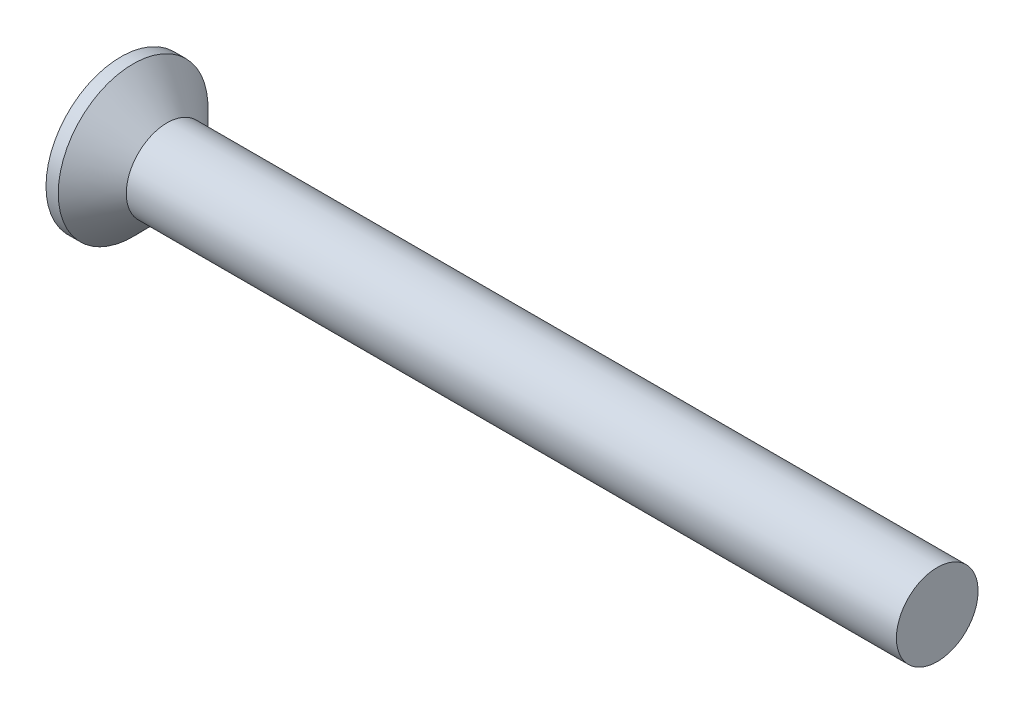
SolidWorks part; units mm, degrees
revolve "Base-Revolve" add sketch "BodySke" angle 360 about L5
sketch "BodySke" plane through (0, 0, 0) normal (0, 0, 1) x (1, 0, 0)
  line L0 (0, 0) -> (0, 2.75)
  line L1 (0, 2.75) -> (0.45, 2.75)
  line L2 (1.7, 1.5) -> (30, 1.5)
  line L3 (30, 1.5) -> (30, 0)
  line L4 (30, 0) -> (0, 0)
  line L5 (-6.35, 0) -> (82.55, 0) construction
  line L6 (1.7, -1.5) -> (30, -1.5) construction
  line L7 (0.45, -2.75) -> (1.7, -1.5) construction
  line L8 (0.45, 2.75) -> (1.7, 1.5)
  line L9 (0, -2.75) -> (0.45, -2.75) construction
  line L10 (2.2, 3.0875) -> (2.2, -6.4375) construction
  line L11 (0, 6.35) -> (0, -3.175) construction
  dimension "Diameter" = 3
  dimension "Length" = 30
  dimension "Head_ht" = 1.7
  dimension "Head_dia" = 5.5
  dimension "Head_ang" = 90
  dimension "D6" = 0.45
  dimension "Advance" = 0.5
  dimension "Thread_nom" = 30
cosmetic thread "ThreadCosmetic" parameters "Thread_length"=27.8, "Thread_minor"=2.439
extrude "Slot" [suppressed] cut sketch "Sketch2" against normal blind 0.9
sketch "Sketch2" plane through (0, 0, 0) normal (-1, 0, 0) x (0, 0, 1)
  line L0 (-2.75, -0.5) -> (2.75, -0.5)
  line L1 (-2.75, -0.5) -> (-2.75, 0.5)
  line L2 (2.75, 0.5) -> (-2.75, 0.5)
  line L3 (2.75, 0.5) -> (2.75, -0.5)
  dimension "Slot_width" = 1
  dimension "D1" = 0.5
  dimension "D2" = 5.5
  dimension "D3" = 2.75
ref_plane "Plane1" through (0, 0, 0) normal (0, 0, 1) x (1, 0, 0)
ref_plane "Plane2" through (0, 0, 0) normal (0, 1, 0) x (1, 0, 0)
ref_plane "Plane3" through (0, 0, 0) normal (1, 0, 0) x (0, 0, -1)
sketch "Sketch3" plane through (0, 0, 0) normal (-1, 0, 0) x (0, 0, 1)
  line L0 (-0.395, 1.55) -> (0.395, 1.55)
  line L1 (0.395, 1.55) -> (0.395, -1.55)
  line L2 (0.395, -1.55) -> (-0.395, -1.55)
  line L3 (-0.395, -1.55) -> (-0.395, 1.55)
  dimension "Cross_dia" = 3.1
  dimension "Cross_width" = 0.79
  dimension "D1" = 1.55
  dimension "D2" = 0.395
ref_plane "Plane4" through (2.08, 0, 0) normal (-1, 0, 0) x (0, 0, 1)
sketch "Sketch4" plane through (2.08, 0, 0) normal (-1, 0, 0) x (0, 0, 1)
  line L0 (-0.1975, 0.1975) -> (0.1975, 0.1975)
  line L3 (0.1975, 0.1975) -> (0.1975, -0.1975)
  line L4 (0.1975, -0.1975) -> (-0.1975, -0.1975)
  line L5 (-0.1975, -0.1975) -> (-0.1975, 0.1975)
  dimension "D2" = 0.395
  dimension "D1" = 0.395
  dimension "D3" = 0.1975
  dimension "D4" = 0.1975
loft "Cross" cut profiles "Sketch3", "Sketch4"
pattern_circular "CirPattern1" count 2 every 90 about axis through (0, 0, 0) along (1, 0, 0) of "Cross"
sketch "ThdSchSke" plane through (0, 0, 0) normal (0, 0, 1) x (1, 0, 0)
  line L0 (2.2, -1.2195) -> (2.0036, -1.5)
  line L1 (2.2, -1.2195) -> (2.3964, -1.5)
  line L2 (2.3964, -1.5) -> (2.3964, -1.875)
  line L3 (-3.175, 0) -> (5.1513, 0) construction
  line L5 (2.3964, -1.875) -> (2.0036, -1.875)
  line L6 (2.0036, -1.875) -> (2.0036, -1.5)
  line L7 (0, 2.75) -> (0, -2.75) construction
  dimension "Diameter" = 3
  dimension "Thread_minor" = 2.439
  dimension "Start" = 2.2
revolve "ThreadSchematic" [suppressed] cut sketch "ThdSchSke" angle 360 about L3
pattern_linear "ThdSchPat" [suppressed]
equation "\"D1@Sketch3\" = \"Cross_dia@Sketch3\" / 2"
equation "\"D2@Sketch3\" = \"Cross_width@Sketch3\" / 2"
equation "\"D1@Sketch4\" = \"Cross_width@Sketch3\" *.5"
equation "\"D2@Sketch4\" = \"D1@Sketch4\""
equation "\"D4@Sketch4\" = \"D2@Sketch4\" / 2"
equation "\"D3@Sketch4\" = \"D1@Sketch4\" / 2"
equation "\"D1@Sketch2\" = \"Slot_width@Sketch2\" / 2"
equation "\"D2@Sketch2\" = \"Head_dia@BodySke\""
equation "\"D3@Sketch2\" = \"D2@Sketch2\" / 2"
equation "\"Thread_length@ThreadCosmetic\" = ((sgn( (\"Length@BodySke\" - \"Advance@BodySke\" - \"Head_ht@BodySke\" ) - \"Thread_nom@BodySke\" )-1)*( (\"Length@BodySke\" - \"Advance@BodySke\" - \"Head_ht@BodySke\" ) - \"Thread_nom@BodySke\" ))/-2+ \"Thread_nom@BodySke\""
equation "\"Thread_minor@ThdSchSke\" = \"Thread_minor@ThreadCosmetic\""
equation "\"Diameter@ThdSchSke\" = \"Diameter@BodySke\""
equation "\"Overcut@ThdSchSke\" = \"Diameter@BodySke\" * 1.25"
equation "\"Start@ThdSchSke\" = 0.000001 + \"Length@BodySke\" - \"Thread_length@ThreadCosmetic\"  '---Countersunk---"
equation "\"Num_threads@ThdSchPat\" = int( \"Thread_length@ThreadCosmetic\" / \"Advance@BodySke\" + 0.999 )  + 1"
equation "\"Advance@ThdSchPat\" = \"Thread_length@ThreadCosmetic\" /  (\"Num_threads@ThdSchPat\" - 1) 'relax it"
